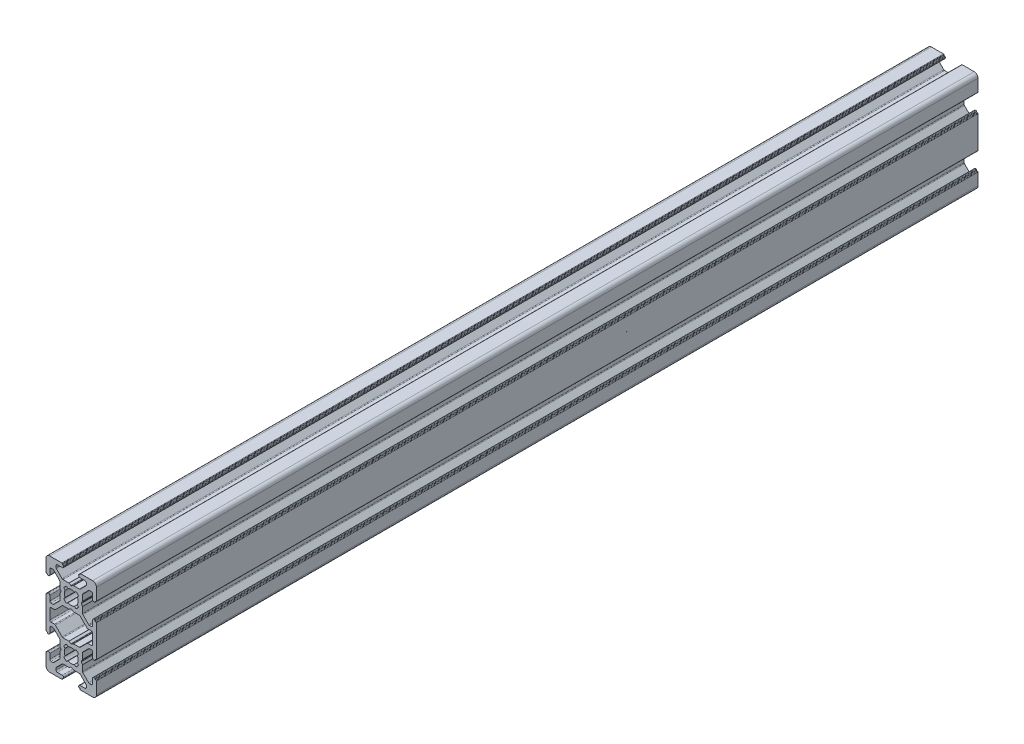
SolidWorks part; units mm, degrees
material "6061-T6 Black anodised"
ref_plane "Front Plane" through (0, 0, 0) normal (0, 0, 1) x (1, 0, 0)
ref_plane "Top Plane" through (0, 0, 0) normal (0, 1, 0) x (1, 0, 0)
ref_plane "Right Plane" through (0, 0, 0) normal (1, 0, 0) x (0, 0, -1)
sketch "Sketch1" plane through (0, 0, 0) normal (0, 0, 1) x (1, 0, 0)
  line L0 (10, -3.75) -> (10, -8.5)
  line L1 (8.5, -3.55) -> (8.5, -5.5)
  line L2 (9.5, -3.25) -> (9.5, -3.35)
  line L3 (9.7, -3.55) -> (9.8, -3.55)
  line L4 (9, -3.05) -> (9.3, -3.05)
  line L5 (9.7, 3.45) -> (9.8, 3.45)
  line L6 (9.5, 3.15) -> (9.5, 3.25)
  line L7 (9, 2.95) -> (9.3, 2.95)
  line L8 (8.5, 3.45) -> (8.5, 5.5)
  line L9 (10, 3.65) -> (10, 10)
  line L10 (-9.7, 3.45) -> (-9.8, 3.45)
  line L11 (-9.5, 3.15) -> (-9.5, 3.25)
  line L12 (-9, 2.95) -> (-9.3, 2.95)
  line L13 (-8.5, 3.45) -> (-8.5, 5.5)
  line L14 (-10, 3.65) -> (-10, 10)
  line L15 (-9.7, -3.55) -> (-9.8, -3.55)
  line L16 (-9.5, -3.25) -> (-9.5, -3.35)
  line L17 (-9, -3.05) -> (-9.3, -3.05)
  line L18 (-8.5, -3.55) -> (-8.5, -5.5)
  line L19 (-10, -3.75) -> (-10, -8.5)
  line L20 (-3.7, -10) -> (-8.5, -10)
  line L21 (-3.5, -8.5) -> (-5.5, -8.5)
  line L22 (-3.2, -9.5) -> (-3.3, -9.5)
  line L23 (-3.5, -9.7) -> (-3.5, -9.8)
  line L24 (-3, -9) -> (-3, -9.3)
  line L25 (3.7, -10) -> (8.5, -10)
  line L26 (3.5, -9.7) -> (3.5, -9.8)
  line L27 (3.2, -9.5) -> (3.3, -9.5)
  line L28 (3, -9) -> (3, -9.3)
  line L29 (3.5, -8.5) -> (5.5, -8.5)
  line L30 (-9.7, 23.5) -> (-9.8, 23.5)
  line L31 (-9.5, 23.2) -> (-9.5, 23.3)
  line L32 (-9, 23) -> (-9.3, 23)
  line L33 (-8.5, 23.5) -> (-8.5, 25.55)
  line L34 (-10, 23.7) -> (-10, 28.5)
  line L35 (-9.7, 16.5) -> (-9.8, 16.5)
  line L36 (-9.5, 16.8) -> (-9.5, 16.7)
  line L37 (-9, 17) -> (-9.3, 17)
  line L38 (-8.5, 16.5) -> (-8.5, 14.55)
  line L39 (-10, 16.3) -> (-10, 10)
  line L40 (10, 16.3) -> (10, 10)
  line L41 (8.5, 16.5) -> (8.5, 14.5)
  line L42 (9.5, 16.8) -> (9.5, 16.7)
  line L43 (9.7, 16.5) -> (9.8, 16.5)
  line L44 (9, 17) -> (9.3, 17)
  line L45 (9.7, 23.5) -> (9.8, 23.5)
  line L46 (9.5, 23.2) -> (9.5, 23.3)
  line L47 (9, 23) -> (9.3, 23)
  line L48 (8.5, 23.5) -> (8.5, 25.5)
  line L49 (10, 23.7) -> (10, 28.5)
  line L50 (-3.7, 30) -> (-8.5, 30)
  line L51 (-3.5, 28.5) -> (-5.5, 28.5)
  line L52 (-3, 29) -> (-3, 29.3)
  line L53 (-3.2, 29.5) -> (-3.3, 29.5)
  line L54 (-3.5, 29.7) -> (-3.5, 29.8)
  line L55 (3.7, 30) -> (8.5, 30)
  line L56 (3.5, 28.5) -> (5.5, 28.5)
  line L57 (3.2, 29.5) -> (3.3, 29.5)
  line L58 (3.5, 29.7) -> (3.5, 29.8)
  line L59 (3, 29) -> (3, 29.3)
  line L60 (2.4453, 18.7418) -> (2.9477, 18.1129)
  line L61 (1.2582, 17.5547) -> (1.8871, 17.0523)
  line L62 (-1.2582, 17.5547) -> (-1.8871, 17.0523)
  line L63 (-2.4453, 18.7418) -> (-2.9477, 18.1129)
  line L64 (-2.4453, 21.2582) -> (-2.9477, 21.8871)
  line L65 (-1.2582, 22.4453) -> (-1.8871, 22.9477)
  line L66 (3.5859, 24.6465) -> (5.8536, 26.9142)
  line L67 (4.6464, 23.5858) -> (6.9142, 25.8536)
  line L68 (4.5, 23.2322) -> (4.5, 20.9536)
  line L69 (4.4732, 20.8536) -> (4.0381, 20.1)
  line L70 (4.4732, 19.1464) -> (4.0381, 19.9)
  line L71 (4.5, 16.7678) -> (4.5, 19.0464)
  line L72 (7.2678, 26) -> (8, 26)
  line L73 (7.2678, 14) -> (8, 14)
  line L74 (2.4453, 21.2582) -> (2.9477, 21.8871)
  line L75 (4.6464, 16.4142) -> (6.9142, 14.1464)
  line L76 (3.2322, 15.5) -> (0.9536, 15.5)
  line L77 (0.8536, 15.5268) -> (0.1, 15.9619)
  line L78 (-0.8536, 15.5268) -> (-0.1, 15.9619)
  line L79 (-3.2322, 15.5) -> (-0.9536, 15.5)
  line L80 (3.5858, 15.3535) -> (6.2929, 12.6464)
  line L81 (-3.5858, 15.3535) -> (-6.2929, 12.6464)
  line L82 (-4.5, 16.7678) -> (-4.5, 19.0464)
  line L83 (-4.4732, 19.1464) -> (-4.0381, 19.9)
  line L84 (-4.4732, 20.8536) -> (-4.0381, 20.1)
  line L85 (-4.5, 23.2322) -> (-4.5, 20.9536)
  line L86 (-7.2178, 14.05) -> (-8, 14.05)
  line L87 (-7.3178, 26.05) -> (-8, 26.05)
  line L88 (-4.6464, 16.4142) -> (-6.8642, 14.1964)
  line L89 (-4.6464, 23.5858) -> (-6.9642, 25.9036)
  line L90 (1.2582, 22.4453) -> (1.8871, 22.9477)
  line L91 (-3.5859, 24.6465) -> (-5.8536, 26.9142)
  line L92 (6, 27.2678) -> (6, 28)
  line L93 (-6, 27.2678) -> (-6, 28)
  line L94 (3.2323, 24.5) -> (0.9537, 24.5)
  line L95 (0.8537, 24.4733) -> (0.1, 24.0381)
  line L96 (-0.8537, 24.4733) -> (-0.1, 24.0381)
  line L97 (-3.2323, 24.5) -> (-0.9537, 24.5)
  line L98 (-3.2322, -4.5) -> (-0.9536, -4.5)
  line L99 (-0.8536, -4.4732) -> (-0.1, -4.0381)
  line L100 (0.8536, -4.4732) -> (0.1, -4.0381)
  line L101 (3.2322, -4.5) -> (0.9536, -4.5)
  line L102 (-6, -7.2678) -> (-6, -8)
  line L103 (6, -7.2678) -> (6, -8)
  line L104 (-3.5858, -4.6464) -> (-5.8536, -6.9142)
  line L105 (1.2582, -2.4453) -> (1.8871, -2.9477)
  line L106 (-4.6464, -3.5858) -> (-6.9142, -5.8536)
  line L107 (-4.6464, 3.5858) -> (-6.9142, 5.8536)
  line L108 (-7.2678, -6) -> (-8, -6)
  line L109 (-7.2678, 6) -> (-8, 6)
  line L110 (-4.5, -3.2322) -> (-4.5, -0.9536)
  line L111 (-4.4732, -0.8536) -> (-4.0381, -0.1)
  line L112 (-4.4732, 0.8536) -> (-4.0381, 0.1)
  line L113 (-4.5, 3.2322) -> (-4.5, 0.9536)
  line L114 (-3.586, 4.6466) -> (-6.2929, 7.3535)
  line L115 (3.586, 4.6466) -> (6.2929, 7.3535)
  line L116 (-3.2324, 4.5001) -> (-0.9538, 4.5001)
  line L117 (-0.8538, 4.4733) -> (-0.1, 4.0381)
  line L118 (0.8538, 4.4733) -> (0.1, 4.0381)
  line L119 (3.2324, 4.5001) -> (0.9538, 4.5001)
  line L120 (4.6464, 3.5858) -> (6.9142, 5.8536)
  line L121 (2.4453, -1.2582) -> (2.9477, -1.8871)
  line L122 (7.2678, 6) -> (8, 6)
  line L123 (7.2678, -6) -> (8, -6)
  line L124 (4.5, 3.2322) -> (4.5, 0.9536)
  line L125 (4.4732, 0.8536) -> (4.0381, 0.1)
  line L126 (4.4732, -0.8536) -> (4.0381, -0.1)
  line L127 (4.5, -3.2322) -> (4.5, -0.9536)
  line L128 (4.6464, -3.5858) -> (6.9142, -5.8536)
  line L129 (3.5858, -4.6464) -> (5.8536, -6.9142)
  line L130 (-1.2582, -2.4453) -> (-1.8871, -2.9477)
  line L131 (-2.4453, -1.2582) -> (-2.9477, -1.8871)
  line L132 (-2.4453, 1.2582) -> (-2.9477, 1.8871)
  line L133 (-1.2582, 2.4453) -> (-1.8871, 2.9477)
  line L134 (1.2582, 2.4453) -> (1.8871, 2.9477)
  line L135 (2.4453, 1.2582) -> (2.9477, 1.8871)
  line L136 (6.6464, 12.5) -> (8, 12.5)
  line L137 (8.5, 8) -> (8.5, 12)
  line L138 (6.6464, 7.5) -> (8, 7.5)
  line L139 (-6.6464, 7.5) -> (-8, 7.5)
  line L140 (-8.5, 8) -> (-8.5, 12)
  line L141 (-6.6464, 12.5) -> (-8, 12.5)
  line L142 (0, 33.3296) -> (0, -13.4112) construction
  line L143 (-17.1897, 10) -> (16.9575, 10) construction
  line L144 (-17.1897, 0) -> (16.9575, 0) construction
  line L145 (-17.1897, 20) -> (16.9575, 20) construction
  arc A0 (9.5, -3.25) -> (9.3, -3.05) centre (9.3, -3.25) ccw
  arc A1 (10, -3.75) -> (9.8, -3.55) centre (9.8, -3.75) ccw
  arc A2 (9.5, -3.35) -> (9.7, -3.55) centre (9.7, -3.35) ccw
  arc A3 (9, -3.05) -> (8.5, -3.55) centre (9, -3.55) ccw
  arc A4 (9.7, 3.45) -> (9.5, 3.25) centre (9.7, 3.25) ccw
  arc A5 (9.8, 3.45) -> (10, 3.65) centre (9.8, 3.65) ccw
  arc A6 (9.3, 2.95) -> (9.5, 3.15) centre (9.3, 3.15) ccw
  arc A7 (8.5, 3.45) -> (9, 2.95) centre (9, 3.45) ccw
  arc A8 (-9.5, 3.25) -> (-9.7, 3.45) centre (-9.7, 3.25) ccw
  arc A9 (-10, 3.65) -> (-9.8, 3.45) centre (-9.8, 3.65) ccw
  arc A10 (-9.5, 3.15) -> (-9.3, 2.95) centre (-9.3, 3.15) ccw
  arc A11 (-9, 2.95) -> (-8.5, 3.45) centre (-9, 3.45) ccw
  arc A12 (-9.7, -3.55) -> (-9.5, -3.35) centre (-9.7, -3.35) ccw
  arc A13 (-9.8, -3.55) -> (-10, -3.75) centre (-9.8, -3.75) ccw
  arc A14 (-9.3, -3.05) -> (-9.5, -3.25) centre (-9.3, -3.25) ccw
  arc A15 (-8.5, -3.55) -> (-9, -3.05) centre (-9, -3.55) ccw
  arc A16 (-3.2, -9.5) -> (-3, -9.3) centre (-3.2, -9.3) ccw
  arc A17 (-3.7, -10) -> (-3.5, -9.8) centre (-3.7, -9.8) ccw
  arc A18 (-3.3, -9.5) -> (-3.5, -9.7) centre (-3.3, -9.7) ccw
  arc A19 (-3, -9) -> (-3.5, -8.5) centre (-3.5, -9) ccw
  arc A20 (3.5, -9.7) -> (3.3, -9.5) centre (3.3, -9.7) ccw
  arc A21 (3.5, -9.8) -> (3.7, -10) centre (3.7, -9.8) ccw
  arc A22 (3, -9.3) -> (3.2, -9.5) centre (3.2, -9.3) ccw
  arc A23 (3.5, -8.5) -> (3, -9) centre (3.5, -9) ccw
  arc A24 (-9.5, 23.3) -> (-9.7, 23.5) centre (-9.7, 23.3) ccw
  arc A25 (-10, 23.7) -> (-9.8, 23.5) centre (-9.8, 23.7) ccw
  arc A26 (-9.5, 23.2) -> (-9.3, 23) centre (-9.3, 23.2) ccw
  arc A27 (-9, 23) -> (-8.5, 23.5) centre (-9, 23.5) ccw
  arc A28 (-9.7, 16.5) -> (-9.5, 16.7) centre (-9.7, 16.7) ccw
  arc A29 (-9.8, 16.5) -> (-10, 16.3) centre (-9.8, 16.3) ccw
  arc A30 (-9.3, 17) -> (-9.5, 16.8) centre (-9.3, 16.8) ccw
  arc A31 (-8.5, 16.5) -> (-9, 17) centre (-9, 16.5) ccw
  arc A32 (9.5, 16.8) -> (9.3, 17) centre (9.3, 16.8) ccw
  arc A33 (10, 16.3) -> (9.8, 16.5) centre (9.8, 16.3) ccw
  arc A34 (9.5, 16.7) -> (9.7, 16.5) centre (9.7, 16.7) ccw
  arc A35 (9, 17) -> (8.5, 16.5) centre (9, 16.5) ccw
  arc A36 (9.7, 23.5) -> (9.5, 23.3) centre (9.7, 23.3) ccw
  arc A37 (9.8, 23.5) -> (10, 23.7) centre (9.8, 23.7) ccw
  arc A38 (9.3, 23) -> (9.5, 23.2) centre (9.3, 23.2) ccw
  arc A39 (8.5, 23.5) -> (9, 23) centre (9, 23.5) ccw
  arc A40 (-3, 29.3) -> (-3.2, 29.5) centre (-3.2, 29.3) ccw
  arc A41 (-3.5, 29.8) -> (-3.7, 30) centre (-3.7, 29.8) ccw
  arc A42 (-3.5, 29.7) -> (-3.3, 29.5) centre (-3.3, 29.7) ccw
  arc A43 (-3.5, 28.5) -> (-3, 29) centre (-3.5, 29) ccw
  arc A44 (3.2, 29.5) -> (3, 29.3) centre (3.2, 29.3) ccw
  arc A45 (3.7, 30) -> (3.5, 29.8) centre (3.7, 29.8) ccw
  arc A46 (3.3, 29.5) -> (3.5, 29.7) centre (3.3, 29.7) ccw
  arc A47 (3, 29) -> (3.5, 28.5) centre (3.5, 29) ccw
  arc A48 (2.4453, 18.7418) -> (2.4453, 21.2582) centre (0, 20) ccw
  arc A49 (-1.2582, 17.5547) -> (1.2582, 17.5547) centre (0, 20) ccw
  arc A50 (-2.4453, 21.2582) -> (-2.4453, 18.7418) centre (0, 20) ccw
  arc A51 (1.8871, 17.0523) -> (2.9477, 18.1129) centre (0, 20) ccw
  arc A52 (-2.9477, 18.1129) -> (-1.8871, 17.0523) centre (0, 20) ccw
  arc A53 (-1.8871, 22.9477) -> (-2.9477, 21.8871) centre (0, 20) ccw
  arc A54 (2.9477, 21.8871) -> (1.8871, 22.9477) centre (0, 20) ccw
  arc A55 (4.0381, 20.1) -> (4.0381, 19.9) centre (4.2113, 20) ccw
  arc A56 (4.5, 19.0464) -> (4.4732, 19.1464) centre (4.3, 19.0464) ccw
  arc A57 (4.4732, 20.8536) -> (4.5, 20.9536) centre (4.3, 20.9536) ccw
  arc A58 (6.9142, 14.1464) -> (7.2678, 14) centre (7.2678, 14.5) ccw
  arc A59 (4.5, 16.7678) -> (4.6464, 16.4142) centre (5, 16.7678) ccw
  arc A60 (4.6464, 23.5858) -> (4.5, 23.2322) centre (5, 23.2322) ccw
  arc A61 (7.2678, 26) -> (6.9142, 25.8536) centre (7.2678, 25.5) ccw
  arc A62 (0.1, 15.9619) -> (-0.1, 15.9619) centre (0, 15.7887) ccw
  arc A63 (-0.9536, 15.5) -> (-0.8536, 15.5268) centre (-0.9536, 15.7) ccw
  arc A64 (0.8536, 15.5268) -> (0.9536, 15.5) centre (0.9536, 15.7) ccw
  arc A65 (-3.2322, 15.5) -> (-3.5858, 15.3535) centre (-3.2322, 15) ccw
  arc A66 (3.5858, 15.3535) -> (3.2322, 15.5) centre (3.2322, 15) ccw
  arc A67 (-4.0381, 19.9) -> (-4.0381, 20.1) centre (-4.2113, 20) ccw
  arc A68 (-4.5, 20.9536) -> (-4.4732, 20.8536) centre (-4.3, 20.9536) ccw
  arc A69 (-4.4732, 19.1464) -> (-4.5, 19.0464) centre (-4.3, 19.0464) ccw
  arc A70 (-6.9642, 25.9036) -> (-7.3178, 26.05) centre (-7.3178, 25.55) ccw
  arc A71 (-4.5, 23.2322) -> (-4.6464, 23.5858) centre (-5, 23.2322) ccw
  arc A72 (-4.6464, 16.4142) -> (-4.5, 16.7678) centre (-5, 16.7678) ccw
  arc A73 (-7.2178, 14.05) -> (-6.8642, 14.1964) centre (-7.2178, 14.55) ccw
  arc A74 (-6, 27.2678) -> (-5.8536, 26.9142) centre (-5.5, 27.2678) ccw
  arc A75 (-3.5859, 24.6465) -> (-3.2323, 24.5) centre (-3.2323, 25) ccw
  arc A76 (3.2323, 24.5) -> (3.5859, 24.6465) centre (3.2323, 25) ccw
  arc A77 (5.8536, 26.9142) -> (6, 27.2678) centre (5.5, 27.2678) ccw
  arc A78 (8.5, 25.5) -> (8, 26) centre (8, 25.5) ccw
  arc A79 (10, 28.5) -> (8.5, 30) centre (8.5, 28.5) ccw
  arc A80 (8, 14) -> (8.5, 14.5) centre (8, 14.5) ccw
  arc A81 (-8.5, 14.55) -> (-8, 14.05) centre (-8, 14.55) ccw
  arc A82 (-8, 26.05) -> (-8.5, 25.55) centre (-8, 25.55) ccw
  arc A83 (6, 28) -> (5.5, 28.5) centre (5.5, 28) ccw
  arc A84 (-8.5, 30) -> (-10, 28.5) centre (-8.5, 28.5) ccw
  arc A85 (-5.5, 28.5) -> (-6, 28) centre (-5.5, 28) ccw
  arc A86 (-0.8537, 24.4733) -> (-0.9537, 24.5) centre (-0.9537, 24.3) ccw
  arc A87 (0.9537, 24.5) -> (0.8537, 24.4733) centre (0.9537, 24.3) ccw
  arc A88 (-0.1, 24.0381) -> (0.1, 24.0381) centre (0, 24.2113) ccw
  arc A89 (1.2582, 22.4453) -> (-1.2582, 22.4453) centre (0, 20) ccw
  arc A90 (-1.2582, -2.4453) -> (1.2582, -2.4453) centre (0, 0) ccw
  arc A91 (0.1, -4.0381) -> (-0.1, -4.0381) centre (0, -4.2113) ccw
  arc A92 (0.8536, -4.4732) -> (0.9536, -4.5) centre (0.9536, -4.3) ccw
  arc A93 (-0.9536, -4.5) -> (-0.8536, -4.4732) centre (-0.9536, -4.3) ccw
  arc A94 (-6, -8) -> (-5.5, -8.5) centre (-5.5, -8) ccw
  arc A95 (-10, -8.5) -> (-8.5, -10) centre (-8.5, -8.5) ccw
  arc A96 (5.5, -8.5) -> (6, -8) centre (5.5, -8) ccw
  arc A97 (-8.5, -5.5) -> (-8, -6) centre (-8, -5.5) ccw
  arc A98 (-8, 6) -> (-8.5, 5.5) centre (-8, 5.5) ccw
  arc A99 (8.5, 5.5) -> (8, 6) centre (8, 5.5) ccw
  arc A100 (8.5, -10) -> (10, -8.5) centre (8.5, -8.5) ccw
  arc A101 (8, -6) -> (8.5, -5.5) centre (8, -5.5) ccw
  arc A102 (6, -7.2678) -> (5.8536, -6.9142) centre (5.5, -7.2678) ccw
  arc A103 (3.5858, -4.6464) -> (3.2322, -4.5) centre (3.2322, -5) ccw
  arc A104 (-3.2322, -4.5) -> (-3.5858, -4.6464) centre (-3.2322, -5) ccw
  arc A105 (-5.8536, -6.9142) -> (-6, -7.2678) centre (-5.5, -7.2678) ccw
  arc A106 (-6.9142, 5.8536) -> (-7.2678, 6) centre (-7.2678, 5.5) ccw
  arc A107 (-4.5, 3.2322) -> (-4.6464, 3.5858) centre (-5, 3.2322) ccw
  arc A108 (-4.6464, -3.5858) -> (-4.5, -3.2322) centre (-5, -3.2322) ccw
  arc A109 (-7.2678, -6) -> (-6.9142, -5.8536) centre (-7.2678, -5.5) ccw
  arc A110 (-4.5, 0.9536) -> (-4.4732, 0.8536) centre (-4.3, 0.9536) ccw
  arc A111 (-4.4732, -0.8536) -> (-4.5, -0.9536) centre (-4.3, -0.9536) ccw
  arc A112 (-4.0381, -0.1) -> (-4.0381, 0.1) centre (-4.2113, 0) ccw
  arc A113 (3.2324, 4.5001) -> (3.586, 4.6466) centre (3.2324, 5.0001) ccw
  arc A114 (-3.586, 4.6466) -> (-3.2324, 4.5001) centre (-3.2324, 5.0001) ccw
  arc A115 (0.9538, 4.5001) -> (0.8538, 4.4733) centre (0.9538, 4.3001) ccw
  arc A116 (-0.8538, 4.4733) -> (-0.9538, 4.5001) centre (-0.9538, 4.3001) ccw
  arc A117 (-0.1, 4.0381) -> (0.1, 4.0381) centre (0, 4.2113) ccw
  arc A118 (6.9142, -5.8536) -> (7.2678, -6) centre (7.2678, -5.5) ccw
  arc A119 (4.5, -3.2322) -> (4.6464, -3.5858) centre (5, -3.2322) ccw
  arc A120 (4.6464, 3.5858) -> (4.5, 3.2322) centre (5, 3.2322) ccw
  arc A121 (7.2678, 6) -> (6.9142, 5.8536) centre (7.2678, 5.5) ccw
  arc A122 (4.5, -0.9536) -> (4.4732, -0.8536) centre (4.3, -0.9536) ccw
  arc A123 (4.4732, 0.8536) -> (4.5, 0.9536) centre (4.3, 0.9536) ccw
  arc A124 (4.0381, 0.1) -> (4.0381, -0.1) centre (4.2113, 0) ccw
  arc A125 (1.8871, -2.9477) -> (2.9477, -1.8871) centre (0, 0) ccw
  arc A126 (-2.9477, -1.8871) -> (-1.8871, -2.9477) centre (0, 0) ccw
  arc A127 (-1.8871, 2.9477) -> (-2.9477, 1.8871) centre (0, 0) ccw
  arc A128 (2.9477, 1.8871) -> (1.8871, 2.9477) centre (0, 0) ccw
  arc A129 (-2.4453, 1.2582) -> (-2.4453, -1.2582) centre (0, 0) ccw
  arc A130 (1.2582, 2.4453) -> (-1.2582, 2.4453) centre (0, 0) ccw
  arc A131 (2.4453, -1.2582) -> (2.4453, 1.2582) centre (0, 0) ccw
  arc A132 (-6.6464, 12.5) -> (-6.2929, 12.6464) centre (-6.6464, 13) ccw
  arc A133 (-8, 12.5) -> (-8.5, 12) centre (-8, 12) ccw
  arc A134 (-8.5, 8) -> (-8, 7.5) centre (-8, 8) ccw
  arc A135 (-6.2929, 7.3535) -> (-6.6464, 7.5) centre (-6.6464, 7) ccw
  arc A136 (6.2929, 12.6464) -> (6.6464, 12.5) centre (6.6464, 13) ccw
  arc A137 (8.5, 12) -> (8, 12.5) centre (8, 12) ccw
  arc A138 (8, 7.5) -> (8.5, 8) centre (8, 8) ccw
  arc A139 (6.6464, 7.5) -> (6.2929, 7.3535) centre (6.6464, 7) ccw
  dimension "D3" = 5.5
  dimension "D4" = 40
  dimension "D17" = 0.5
  dimension "D18" = 1.5
  dimension "D2" = 20
  dimension "D5" = 10
  dimension "D6" = 20
  dimension "D7" = 6
  dimension "D8" = 6
  dimension "D9" = 6
  dimension "D10" = 10
  dimension "D11" = 12
  dimension "D12" = 12
  dimension "D13" = 12
  dimension "D14" = 12
  dimension "D15" = 12
  dimension "D16" = 12
extrude "Extrude1" add sketch "Sketch1" along normal blind 350
